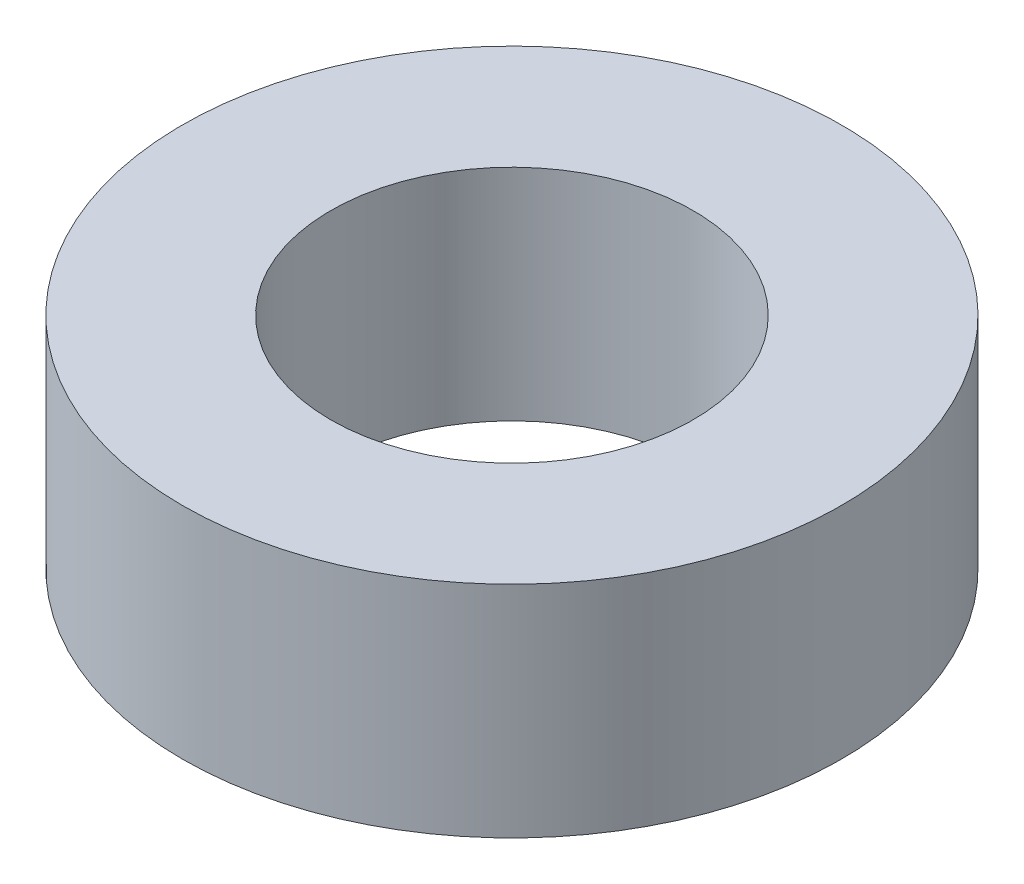
SolidWorks part; units mm, degrees
ref_plane "Front Plane" through (0, 0, 0) normal (0, 0, 1) x (1, 0, 0)
ref_plane "Top Plane" through (0, 0, 0) normal (0, 1, 0) x (1, 0, 0)
ref_plane "Right Plane" through (0, 0, 0) normal (1, 0, 0) x (0, 0, -1)
sketch "Sketch1" plane through (0, 0, 0) normal (0, 1, 0) x (1, 0, 0)
  circle A0 centre (0, 0) radius 1.65
  circle A1 centre (0, 0) radius 3
  dimension "D1" = 3.3
  dimension "D2" = 6
extrude "Boss-Extrude3" add sketch "Sketch1" along normal blind 2
